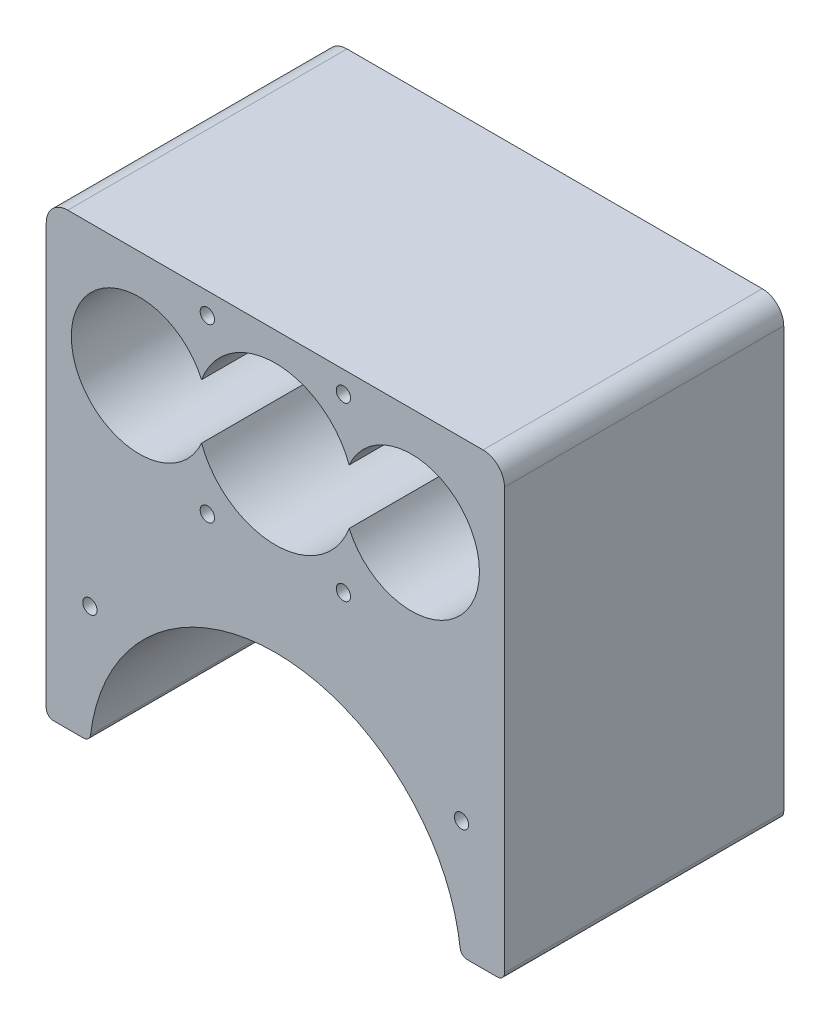
SolidWorks part; units mm, degrees
ref_plane "Спереди" through (0, 0, 0) normal (0, 0, 1) x (1, 0, 0)
ref_plane "Сверху" through (0, 0, 0) normal (0, 1, 0) x (1, 0, 0)
ref_plane "Справа" through (0, 0, 0) normal (1, 0, 0) x (0, 0, -1)
sketch "Эскиз1" plane through (0, 0, 0) normal (0, 0, 1) x (1, 0, 0)
  line L2 (-32, -17) -> (-32, 12)
  line L3 (-29, 15) -> (29, 15)
  line L4 (32, -17) -> (32, 12)
  line L11 (-32, -17) -> (-32, -46.7536)
  line L12 (-31, -47.7536) -> (-26.8041, -47.7536)
  line L13 (32, -17) -> (32, -46.7536)
  line L14 (31, -47.7536) -> (26.8041, -47.7536)
  line L15 (-9.5, 12) -> (9.5, 12) construction
  line L16 (-9.5, 12) -> (-9.5, -12) construction
  line L17 (-9.5, -12) -> (9.5, -12) construction
  line L18 (9.5, 12) -> (9.5, -12) construction
  arc A0 (-10.3092, -3.8367) -> (10.3092, -3.8367) centre (0, 0) ccw
  arc A1 (-10.3092, 3.8367) -> (-10.3092, -3.8367) centre (-19, 0) ccw
  arc A2 (10.3092, -3.8367) -> (10.3092, 3.8367) centre (19, 0) ccw
  arc A4 (29, 15) -> (32, 12) centre (29, 12) cw
  arc A5 (-32, 12) -> (-29, 15) centre (-29, 12) cw
  arc A6 (25.8114, -46.8739) -> (-25.8114, -46.8739) centre (0, -50) ccw
  arc A25 (10.3092, 3.8367) -> (-10.3092, 3.8367) centre (0, 0) ccw
  arc A26 (-32, -46.7536) -> (-31, -47.7536) centre (-31, -46.7536) ccw
  arc A27 (-25.8114, -46.8739) -> (-26.8041, -47.7536) centre (-26.8041, -46.7536) cw
  arc A28 (32, -46.7536) -> (31, -47.7536) centre (31, -46.7536) cw
  arc A29 (26.8041, -47.7536) -> (25.8114, -46.8739) centre (26.8041, -46.7536) cw
  circle A30 centre (-9.5, 12) radius 1
  circle A31 centre (9.5, 12) radius 1
  circle A32 centre (9.5, -12) radius 1
  circle A33 centre (-9.5, -12) radius 1
  circle A34 centre (-25.9028, -31.359) radius 1
  circle A35 centre (26, -31.359) radius 1
  point P54 (0, 0)
  dimension "D1" = 19
  dimension "D3" = 22
  dimension "D4" = 22.5
  dimension "D5" = 3
  dimension "D6" = 64
  dimension "D9" = 3
  dimension "D2" = 19
  dimension "D8" = 15
extrude "Бобышка-Вытянуть1" add sketch "Эскиз1" along normal blind 39
